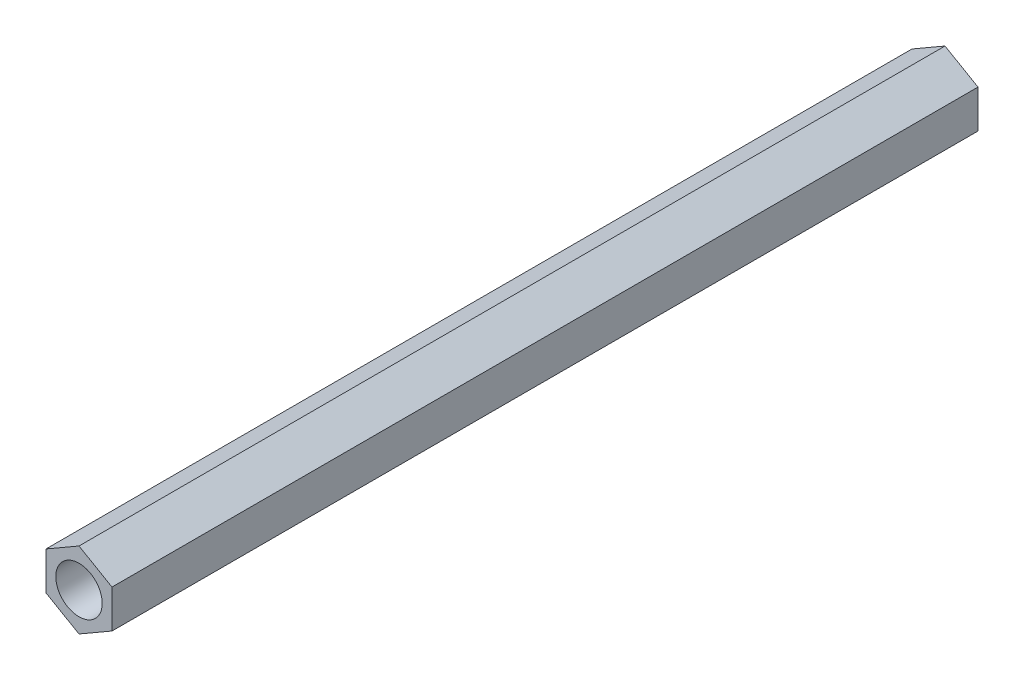
SolidWorks part; units mm, degrees
ref_plane "前视基准面" through (0, 0, 0) normal (0, 0, 1) x (1, 0, 0)
ref_plane "上视基准面" through (0, 0, 0) normal (0, 1, 0) x (1, 0, 0)
ref_plane "右视基准面" through (0, 0, 0) normal (1, 0, 0) x (0, 0, -1)
sketch "草图1" plane through (0, 0, 0) normal (0, 0, 1) x (1, 0, 0)
  line L1 (0, 2.4639) -> (-2.1338, 1.232)
  line L2 (-2.1338, 1.232) -> (-2.1338, -1.232)
  line L3 (-2.1338, -1.232) -> (0, -2.4639)
  line L4 (0, -2.4639) -> (2.1338, -1.232)
  line L5 (2.1338, -1.232) -> (2.1338, 1.232)
  line L6 (2.1338, 1.232) -> (0, 2.4639)
  circle A0 centre (0, 0) radius 1.5
  circle A1 centre (0, 0) radius 2.1338 construction
extrude "凸台-拉伸1" add sketch "草图1" along normal blind 56
